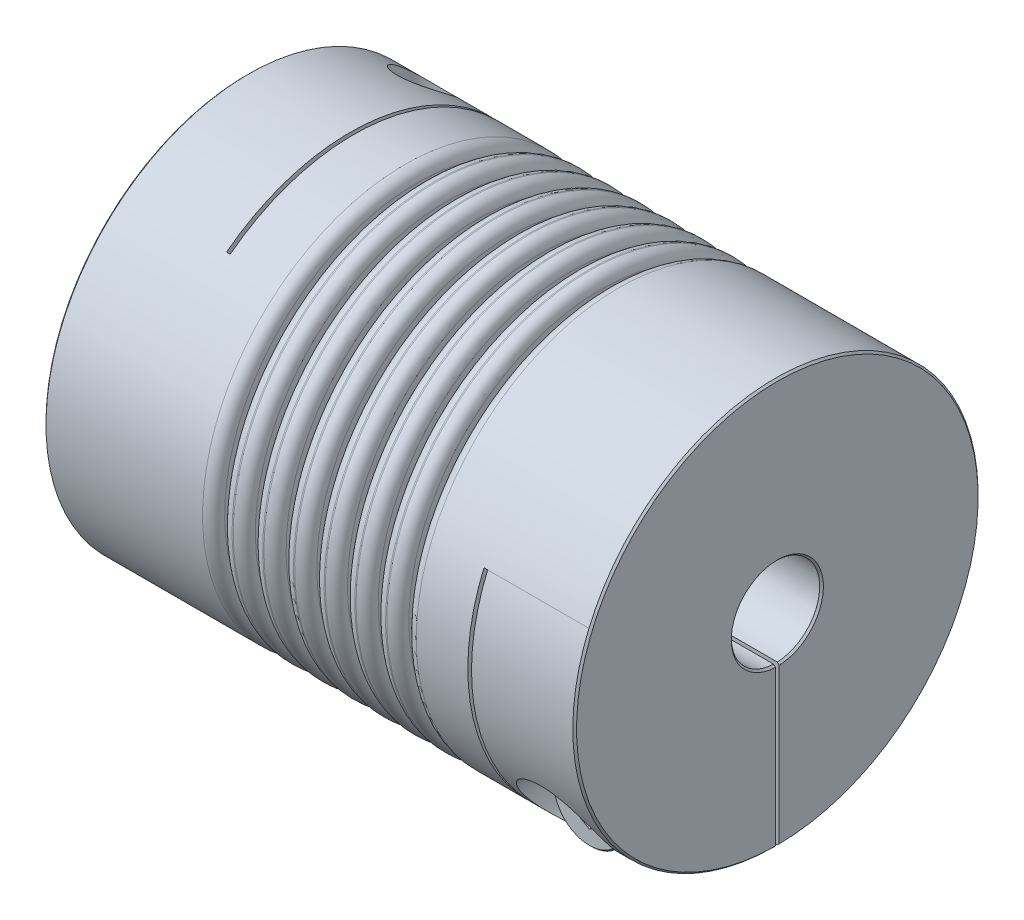
SolidWorks part; units mm, degrees
ref_plane "Front Plane" through (0, 0, 0) normal (0, 0, 1) x (1, 0, 0)
ref_plane "Top Plane" through (0, 0, 0) normal (0, 1, 0) x (1, 0, 0)
ref_plane "Right Plane" through (0, 0, 0) normal (1, 0, 0) x (0, 0, -1)
sketch "Sketch1" plane through (0, 0, 0) normal (1, 0, 0) x (0, 0, -1)
  circle A0 centre (0, 0) radius 27.5
  dimension "dim D" = 55
extrude "Boss-Extrude1" add sketch "Sketch1" along normal mid plane 72
sketch "Sketch2" plane through (36, 0, 0) normal (1, 0, 0) x (0, 0, -1)
  circle A0 centre (0, 0) radius 6
  dimension "dim D1" = 12
extrude "Cut-Extrude1" cut sketch "Sketch2" against normal through all
chamfer "Chamfer1" distance 0.254 angle 45 4 edges at (-36, 0, -6) (-36, 0, -27.5) (36, 0, -27.5) (36, 0, -6)
ref_plane "Plane2" through (0, -27.5, 0) normal (0, -1, 0) x (1, 0, 0)
ref_plane "F" through (-29, 0, 0) normal (-1, 0, 0) x (0, 0, 1)
sketch "Sketch4" plane through (0, -27.5, 0) normal (0, -1, 0) x (1, 0, 0)
  line L0 (-35.746, -27.5) -> (35.746, -27.5) construction
  line L1 (-22, -27.5) -> (-21.5, -27.5)
  line L2 (-22, -27.5) -> (-22, 16.75)
  line L3 (-22, 16.75) -> (-21.5, 16.75)
  line L4 (-21.5, -27.5) -> (-21.5, 16.75)
  line L5 (-22, 6) -> (-22, 27.5) construction
  line L6 (35.746, 6) -> (-35.746, 6) construction
  line L7 (35.746, 27.5) -> (-35.746, 27.5) construction
  line L10 (-22, 16.75) -> (-36, 16.75) construction
  line L11 (-36, 27.246) -> (-36, -27.246) construction
  line L12 (-29, 10.2256) -> (-29, -10.2256) construction
  point P16 (-29, 16.75)
  dimension "D1" = 0.5
extrude "Cut-Extrude2" cut sketch "Sketch4" against normal through all
ref_plane "Plane4" through (0, 0, -27.5) normal (0, 0, -1) x (-1, 0, 0)
sketch "Sketch7" plane through (0, 0, -27.5) normal (0, 0, -1) x (-1, 0, 0)
  line L1 (-21.5, -27.5) -> (-22, -27.5)
  line L2 (-22, -27.5) -> (-22, 10.75)
  line L3 (-22, 10.75) -> (-21.5, 10.75)
  line L4 (-21.5, -27.5) -> (-21.5, 10.75)
  line L5 (36, 8.6487) -> (29, 8.6487) construction
  line L7 (-10.505, -27.5) -> (10.505, -27.5) construction
  line L8 (-35.746, -6) -> (21.5, -6) construction
  line L9 (36, -27.246) -> (36, 27.246) construction
  line L10 (-35.746, -6) -> (21.5, -6) construction
  line L11 (21.5, 21.8103) -> (22, 21.8103) construction
  line L12 (-22, 10.75) -> (-22, -27.5) construction
  line L14 (-35.746, -6) -> (21.5, -6) construction
  line L16 (-35.746, -6) -> (21.5, -6) construction
  line L17 (22, -27.5) -> (35.746, -27.5) construction
  line L18 (29, -10.2256) -> (29, 10.2256) construction
  line L19 (-35.746, -27.5) -> (-35.746, 27.5) construction
  line L20 (-36, 10.75) -> (-29, 10.75) construction
  line L21 (-36, 27.246) -> (-36, -27.246) construction
  line L22 (-29, 10.75) -> (-22, 10.75) construction
  line L23 (-35.746, -27.5) -> (-35.746, 27.5) construction
  line L24 (-35.746, -6) -> (-35.746, 27.5) construction
  line L25 (-35.746, -6) -> (21.5, -6) construction
  point P23 (-22, 10.75)
  point P33 (-35.746, 10.75)
extrude "Cut-Extrude3" cut sketch "Sketch7" against normal through all
sketch "Sketch8" plane through (0, 0, 0) normal (0, 1, 0) x (1, 0, 0)
  line L0 (-22, -16.75) -> (-22, 27.5) construction
  line L1 (-36, 27.5) -> (-22, 27.5)
  line L2 (-36, 27.5) -> (-36, 0)
  line L3 (-36, 0) -> (-22, 0)
  line L4 (-22, 27.5) -> (-22, 0)
  line L5 (10.505, 27.5) -> (-10.505, 27.5) construction
  line L6 (-36, 27.246) -> (-36, -27.246) construction
extrude "Cut-Extrude5" cut sketch "Sketch8" against normal mid plane 0.5
sketch "Sketch13" plane through (0, 0, 0) normal (0, 0, 1) x (1, 0, 0)
  line L0 (36, -27.246) -> (36, 27.246) construction
  line L1 (22, -27.5) -> (36, -27.5)
  line L2 (22, -27.5) -> (22, 0)
  line L3 (22, 0) -> (36, 0)
  line L4 (36, -27.5) -> (36, 0)
extrude "Cut-Extrude6" cut sketch "Sketch13" against normal mid plane 0.5
hole_wizard "CBORE for M6 SHCS2" positions "Sketch12" profile "Sketch11" counterbore size "M6" standard "Ansi Metric" end condition through all
sketch "Sketch12" plane through (0, -27.5, 0) normal (0, -1, 0) x (1, 0, 0)
  line L0 (-29, 10.2256) -> (-29, -10.2256) construction
  line L1 (-22, -5.9948) -> (-22, -27.4989) construction
  line L2 (-22, -5.9948) -> (-22, -27.4989)
  line L3 (-22, -16.7468) -> (-29, -16.7468) construction
  point P0 (-29, -16.7468)
sketch "Sketch11" plane through (-29, -27.5, -16.7468) normal (1, 0, 0) x (0, 0, -1)
  line L0 (0, 0) -> (0, 55)
  line L1 (0, 55) -> (3.3, 55)
  line L3 (3.3, 55) -> (3.3, 15)
  line L4 (3.3, 15) -> (5.5, 15)
  line L5 (5.5, 15) -> (5.5, 0)
  line L7 (5.5, 0) -> (0, 0)
  line L11 (0, -6.35) -> (0, 107.95) construction
  dimension "Thru Hole Dia." = 6.6
  dimension "Thru Hole Depth" = 55
  dimension "C'Bore Dia." = 11
  dimension "C'Bore Depth" = 15
ref_plane "Plane5" through (0, 0, 27.5) normal (0, 0, 1) x (1, 0, 0)
hole_wizard "CBORE for M6 SHCS1" positions "Sketch15" profile "Sketch14" counterbore size "M6" standard "Ansi Metric" end condition through all
sketch "Sketch15" plane through (0, 0, 27.5) normal (0, 0, 1) x (1, 0, 0)
  line L0 (-34.5, -12.5) -> (-23.5, -12.5) construction
  line L1 (-34.5, -12.5) -> (-23.5, -12.5)
  line L5 (0, 0) -> (0, 27.5) construction
  line L6 (-22, 27.5) -> (-35.746, 27.5) construction
  line L8 (34.5, -12.5) -> (23.5, -12.5)
  line L9 (29, -12.5) -> (29, -16.7468) construction
  line L11 (29, -27.4989) -> (29, -5.9948) construction
  line L12 (35.746, -27.4989) -> (22, -27.4989) construction
  line L13 (22, -5.9948) -> (35.746, -5.9948) construction
  point P0 (29, -16.7468)
sketch "Sketch14" plane through (29, -16.7468, 27.5) normal (1, 0, 0) x (0, -1, 0)
  line L0 (0, 0) -> (0, 55)
  line L1 (0, 55) -> (3.3, 55)
  line L3 (3.3, 55) -> (3.3, 15)
  line L4 (3.3, 15) -> (5.5, 15)
  line L5 (5.5, 15) -> (5.5, 0)
  line L7 (5.5, 0) -> (0, 0)
  line L11 (0, -6.35) -> (0, 107.95) construction
  dimension "Thru Hole Dia." = 6.6
  dimension "Thru Hole Depth" = 55
  dimension "C'Bore Dia." = 11
  dimension "C'Bore Depth" = 15
sketch "Sketch16" plane through (0, 0, 12.5) normal (0, 0, 1) x (1, 0, 0)
  circle A0 centre (29, -16.7468) radius 5
  dimension "screw dia" = 10
extrude "Boss-Extrude2" add sketch "Sketch16" along normal blind 6 separate body
sketch "Sketch17" plane through (0, 0, 12.5) normal (0, 0, -1) x (-1, 0, 0)
  circle A0 centre (-29, -16.7468) radius 1.25
  dimension "D1" = 2.5
extrude "Boss-Extrude3" add sketch "Sketch17" along normal blind 8
chamfer "Chamfer2" distance 0.2 angle 45 3 edges at (27.75, -16.7468, 4.5) (34, -16.7468, 12.5) (34, -16.7468, 18.5)
sketch "Sketch18" plane through (0, 0, 18.5) normal (0, 0, 1) x (1, 0, 0)
  line L1 (29, -19.6336) -> (31.5, -18.1902)
  line L2 (31.5, -18.1902) -> (31.5, -15.3035)
  line L3 (31.5, -15.3035) -> (29, -13.8601)
  line L4 (29, -13.8601) -> (26.5, -15.3035)
  line L5 (26.5, -15.3035) -> (26.5, -18.1902)
  line L6 (26.5, -18.1902) -> (29, -19.6336)
  circle A0 centre (29, -16.7468) radius 2.5 construction
  dimension "hex" = 5
extrude "Cut-Extrude7" cut sketch "Sketch18" against normal blind 1.5
mirror "Mirror1" about plane through (0, 0, 0) normal (1, 0, 0) of bodies 121
pattern_circular "CirPattern1" count 2 every 90 about axis through (0, 0, 0) along (1, 0, 0) of bodies 122 117
delete or keep bodies "Body-Delete1" type delete bodies bodies 122
sketch "Sketch19" plane through (0, 0, 0) normal (0, 0, 1) x (1, 0, 0)
  line L0 (-36, -20) -> (36, -20) construction
  line L1 (-36, 27.246) -> (-36, -27.246) construction
  line L2 (36, -27.2449) -> (36, 27.246) construction
  line L3 (0, 0) -> (0, -20) construction
  line L4 (0, 0) -> (0, 20) construction
  line L5 (35.746, 27.5) -> (-21.5, 27.5) construction
  line L6 (-0.5, 27.5) -> (0.5, 27.5)
  line L7 (-0.5, 27.5) -> (-0.5, 20)
  line L8 (-0.5, 20) -> (0.5, 20)
  line L9 (0.5, 27.5) -> (0.5, 20)
  line L10 (3.6667, 27.5) -> (4.6667, 27.5)
  line L11 (3.6667, 27.5) -> (3.6667, 20)
  line L12 (3.6667, 20) -> (4.6667, 20)
  line L13 (4.6667, 27.5) -> (4.6667, 20)
  line L14 (7.8333, 27.5) -> (8.8333, 27.5)
  line L15 (7.8333, 27.5) -> (7.8333, 20)
  line L16 (7.8333, 20) -> (8.8333, 20)
  line L17 (8.8333, 27.5) -> (8.8333, 20)
  line L18 (12, 27.5) -> (13, 27.5)
  line L19 (12, 27.5) -> (12, 20)
  line L20 (12, 20) -> (13, 20)
  line L21 (13, 27.5) -> (13, 20)
  line L22 (-13, 27.5) -> (-13, 20)
  line L23 (-12, 20) -> (-13, 20)
  line L24 (-12, 27.5) -> (-12, 20)
  line L25 (-12, 27.5) -> (-13, 27.5)
  line L26 (-8.8333, 27.5) -> (-8.8333, 20)
  line L27 (-7.8333, 20) -> (-8.8333, 20)
  line L28 (-7.8333, 27.5) -> (-7.8333, 20)
  line L29 (-7.8333, 27.5) -> (-8.8333, 27.5)
  line L30 (-4.6667, 27.5) -> (-4.6667, 20)
  line L31 (-3.6667, 20) -> (-4.6667, 20)
  line L32 (-3.6667, 27.5) -> (-3.6667, 20)
  line L33 (-3.6667, 27.5) -> (-4.6667, 27.5)
  line L34 (0, 0) -> (-36, 0) construction
  dimension "D1" = 1
  dimension "Dim E" = 40
  dimension "Dim L1" = 23
  dimension "D2" = 4
revolve "Cut-Revolve1" cut sketch "Sketch19" angle 360 about L34
fillet "Fillet1" radius 1.5 14 edges at (-12, 27.5, 0) (-8.8333, 27.5, 0) (-7.8333, 27.5, 0) (-4.6667, 27.5, 0) (-0.5, 27.5, 0) (-3.6667, 27.5, 0) (0.5, 27.5, 0) (3.6667, 27.5, 0) (4.6667, 27.5, 0) (7.8333, 27.5, 0) (8.8333, 27.5, 0) (12, 27.5, 0) (13, 27.5, 0) (-13, 27.5, 0)
fillet "Fillet2" radius 0.1 14 edges at (12, 20, 0) (13, 20, 0) (7.8333, 20, 0) (8.8333, 20, 0) (3.6667, 20, 0) (4.6667, 20, 0) (-0.5, 20, 0) (0.5, 20, 0) (-4.6667, 20, 0) (-3.6667, 20, 0) (-8.8333, 20, 0) (-7.8333, 20, 0) (-13, 20, 0) (-12, 20, 0)
